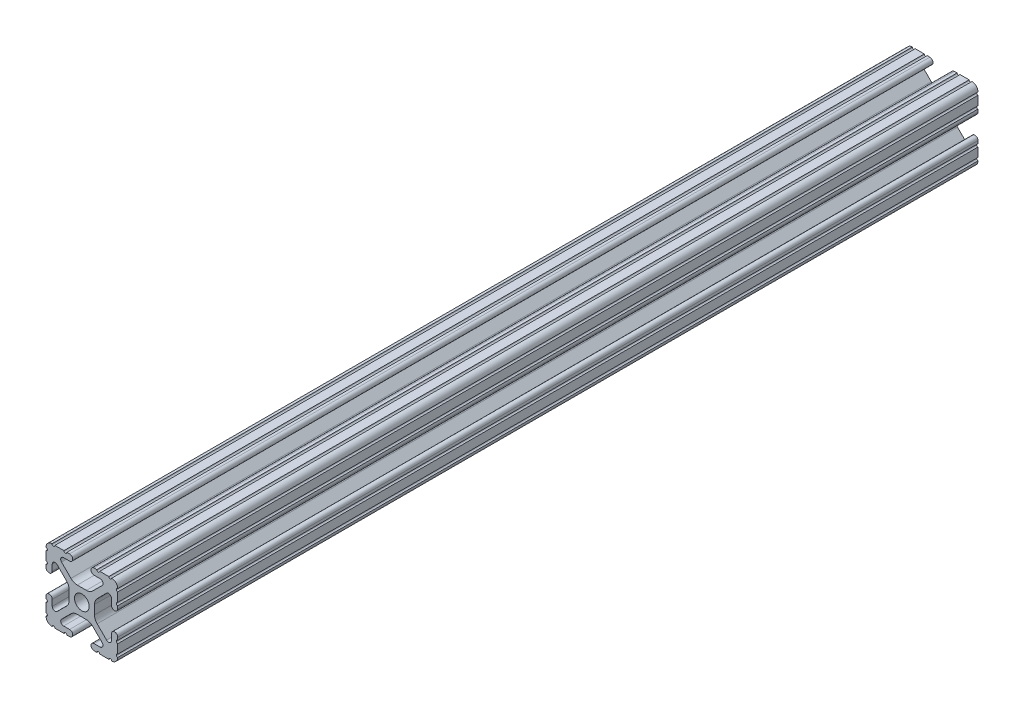
SolidWorks part; units mm, degrees
ref_plane "Front Plane" through (0, 0, 0) normal (0, 0, 1) x (1, 0, 0)
ref_plane "Top Plane" through (0, 0, 0) normal (0, 1, 0) x (1, 0, 0)
ref_plane "Right Plane" through (0, 0, 0) normal (1, 0, 0) x (0, 0, -1)
ref_plane "Plane1" through (0, 0, -1270) normal (0, 0, -1) x (-1, 0, 0)
sketch "Sketch1" plane through (0, 0, -1270) normal (0, 0, -1) x (-1, 0, 0)
  line L0 (12.7, -9.5504) -> (12.7, -6.3331)
  line L1 (12.7, -5.3171) -> (12.7, -4.3434)
  line L2 (10.4902, -4.3434) -> (10.4902, -6.4748)
  line L3 (8.7558, -7.1932) -> (5.4257, -3.8632)
  line L4 (4.4958, -1.6181) -> (4.4958, 1.6181)
  line L5 (5.4257, 3.8632) -> (8.7558, 7.1932)
  line L6 (10.4902, 6.4748) -> (10.4902, 4.3434)
  line L7 (12.7, 4.3434) -> (12.7, 5.3171)
  line L8 (12.7, 6.3331) -> (12.7, 9.5504)
  line L9 (9.5504, 12.7) -> (6.3331, 12.7)
  line L10 (5.3171, 12.7) -> (4.3434, 12.7)
  line L11 (4.3434, 10.4902) -> (6.4748, 10.4902)
  line L12 (7.1932, 8.7558) -> (3.8632, 5.4257)
  line L13 (1.6181, 4.4958) -> (-1.6181, 4.4958)
  line L14 (-3.8632, 5.4257) -> (-7.1932, 8.7558)
  line L15 (-6.4748, 10.4902) -> (-4.3434, 10.4902)
  line L16 (-4.3434, 12.7) -> (-5.3171, 12.7)
  line L17 (-6.3331, 12.7) -> (-9.5504, 12.7)
  line L18 (-12.7, 9.5504) -> (-12.7, 6.3331)
  line L19 (-12.7, 5.3171) -> (-12.7, 4.3434)
  line L20 (-10.4902, 4.3434) -> (-10.4902, 6.4748)
  line L21 (-8.7558, 7.1932) -> (-5.4257, 3.8632)
  line L22 (-4.4958, 1.6181) -> (-4.4958, -1.6181)
  line L23 (-5.4257, -3.8632) -> (-8.7558, -7.1932)
  line L24 (-10.4902, -6.4748) -> (-10.4902, -4.3434)
  line L25 (-12.7, -4.3434) -> (-12.7, -5.3171)
  line L26 (-12.7, -6.3331) -> (-12.7, -9.5504)
  line L27 (-9.5504, -12.7) -> (-6.3331, -12.7)
  line L28 (-5.3171, -12.7) -> (-4.3434, -12.7)
  line L29 (-4.3434, -10.4902) -> (-6.4748, -10.4902)
  line L30 (-7.1932, -8.7558) -> (-3.8632, -5.4257)
  line L31 (-1.6181, -4.4958) -> (1.6181, -4.4958)
  line L32 (3.8632, -5.4257) -> (7.1932, -8.7558)
  line L33 (6.4748, -10.4902) -> (4.3434, -10.4902)
  line L34 (4.3434, -12.7) -> (5.3171, -12.7)
  line L35 (6.3331, -12.7) -> (9.5504, -12.7)
  circle A0 centre (0, 0) radius 2.6035
  arc A1 (12.7, -6.3331) -> (12.7, -5.3171) centre (12.7, -5.8251) cw
  arc A2 (12.7, -4.3434) -> (10.4902, -4.3434) centre (11.5951, -4.3434) ccw
  arc A3 (10.4902, -6.4748) -> (8.7558, -7.1932) centre (9.4742, -6.4748) cw
  arc A4 (5.4257, -3.8632) -> (4.4958, -1.6181) centre (7.6708, -1.6181) cw
  arc A5 (4.4958, 1.6181) -> (5.4257, 3.8632) centre (7.6708, 1.6181) cw
  arc A6 (8.7558, 7.1932) -> (10.4902, 6.4748) centre (9.4742, 6.4748) cw
  arc A7 (10.4902, 4.3434) -> (12.7, 4.3434) centre (11.5951, 4.3434) ccw
  arc A8 (12.7, 5.3171) -> (12.7, 6.3331) centre (12.7, 5.8251) cw
  arc A9 (12.7, 9.5504) -> (12.6998, 10.5664) centre (12.7, 10.0584) cw
  arc A10 (12.6998, 10.5664) -> (10.5664, 12.6998) centre (10.5918, 10.5918) ccw
  arc A11 (10.5664, 12.6998) -> (9.5504, 12.7) centre (10.0584, 12.7) cw
  arc A12 (6.3331, 12.7) -> (5.3171, 12.7) centre (5.8251, 12.7) cw
  arc A13 (4.3434, 12.7) -> (4.3434, 10.4902) centre (4.3434, 11.5951) ccw
  arc A14 (6.4748, 10.4902) -> (7.1932, 8.7558) centre (6.4748, 9.4742) cw
  arc A15 (3.8632, 5.4257) -> (1.6181, 4.4958) centre (1.6181, 7.6708) cw
  arc A16 (-1.6181, 4.4958) -> (-3.8632, 5.4257) centre (-1.6181, 7.6708) cw
  arc A17 (-7.1932, 8.7558) -> (-6.4748, 10.4902) centre (-6.4748, 9.4742) cw
  arc A18 (-4.3434, 10.4902) -> (-4.3434, 12.7) centre (-4.3434, 11.5951) ccw
  arc A19 (-5.3171, 12.7) -> (-6.3331, 12.7) centre (-5.8251, 12.7) cw
  arc A20 (-9.5504, 12.7) -> (-10.5664, 12.6998) centre (-10.0584, 12.7) cw
  arc A21 (-10.5664, 12.6998) -> (-12.6998, 10.5664) centre (-10.5918, 10.5918) ccw
  arc A22 (-12.6998, 10.5664) -> (-12.7, 9.5504) centre (-12.7, 10.0584) cw
  arc A23 (-12.7, 6.3331) -> (-12.7, 5.3171) centre (-12.7, 5.8251) cw
  arc A24 (-12.7, 4.3434) -> (-10.4902, 4.3434) centre (-11.5951, 4.3434) ccw
  arc A25 (-10.4902, 6.4748) -> (-8.7558, 7.1932) centre (-9.4742, 6.4748) cw
  arc A26 (-5.4257, 3.8632) -> (-4.4958, 1.6181) centre (-7.6708, 1.6181) cw
  arc A27 (-4.4958, -1.6181) -> (-5.4257, -3.8632) centre (-7.6708, -1.6181) cw
  arc A28 (-8.7558, -7.1932) -> (-10.4902, -6.4748) centre (-9.4742, -6.4748) cw
  arc A29 (-10.4902, -4.3434) -> (-12.7, -4.3434) centre (-11.5951, -4.3434) ccw
  arc A30 (-12.7, -5.3171) -> (-12.7, -6.3331) centre (-12.7, -5.8251) cw
  arc A31 (-12.7, -9.5504) -> (-12.6998, -10.5664) centre (-12.7, -10.0584) cw
  arc A32 (-12.6998, -10.5664) -> (-10.5664, -12.6998) centre (-10.5918, -10.5918) ccw
  arc A33 (-10.5664, -12.6998) -> (-9.5504, -12.7) centre (-10.0584, -12.7) cw
  arc A34 (-6.3331, -12.7) -> (-5.3171, -12.7) centre (-5.8251, -12.7) cw
  arc A35 (-4.3434, -12.7) -> (-4.3434, -10.4902) centre (-4.3434, -11.5951) ccw
  arc A36 (-6.4748, -10.4902) -> (-7.1932, -8.7558) centre (-6.4748, -9.4742) cw
  arc A37 (-3.8632, -5.4257) -> (-1.6181, -4.4958) centre (-1.6181, -7.6708) cw
  arc A38 (1.6181, -4.4958) -> (3.8632, -5.4257) centre (1.6181, -7.6708) cw
  arc A39 (7.1932, -8.7558) -> (6.4748, -10.4902) centre (6.4748, -9.4742) cw
  arc A40 (4.3434, -10.4902) -> (4.3434, -12.7) centre (4.3434, -11.5951) ccw
  arc A41 (5.3171, -12.7) -> (6.3331, -12.7) centre (5.8251, -12.7) cw
  arc A42 (9.5504, -12.7) -> (10.5664, -12.6998) centre (10.0584, -12.7) cw
  arc A43 (10.5664, -12.6998) -> (12.6998, -10.5664) centre (10.5918, -10.5918) ccw
  arc A44 (12.6998, -10.5664) -> (12.7, -9.5504) centre (12.7, -10.0584) cw
extrude "Boss-Extrude1" add sketch "Sketch1" against normal blind 1270
ref_plane "Plane2" through (0, 0, -698.5) normal (0, 0, -1) x (-1, 0, 0)
sketch "Sketch6" plane through (0, 0, -698.5) normal (0, 0, -1) x (-1, 0, 0)
  line L0 (79.0024, -75.2236) -> (-43.6645, -75.2236)
  line L1 (79.0024, -75.2236) -> (79.0024, 34.1242)
  line L2 (79.0024, 34.1242) -> (-43.6645, 34.1242)
  line L3 (-43.6645, -75.2236) -> (-43.6645, 34.1242)
extrude "Cut-Extrude1" cut sketch "Sketch6" along normal through all
sketch "Sketch7" plane through (0, 0, -698.5) normal (0, 0, -1) x (-1, 0, 0)
  line L5 (-19.4997, 15.6935) -> (19.4997, 15.6935)
  line L6 (-19.4997, 15.6935) -> (-19.4997, -15.6935)
  line L7 (-19.4997, -15.6935) -> (19.4997, -15.6935)
  line L8 (19.4997, 15.6935) -> (19.4997, -15.6935)
  line L9 (-19.4997, 15.6935) -> (19.4997, -15.6935) construction
  line L10 (-19.4997, -15.6935) -> (19.4997, 15.6935) construction
  point P0 (0, 0)
extrude "Cut-Extrude2" cut sketch "Sketch7" against normal blind 393.7
